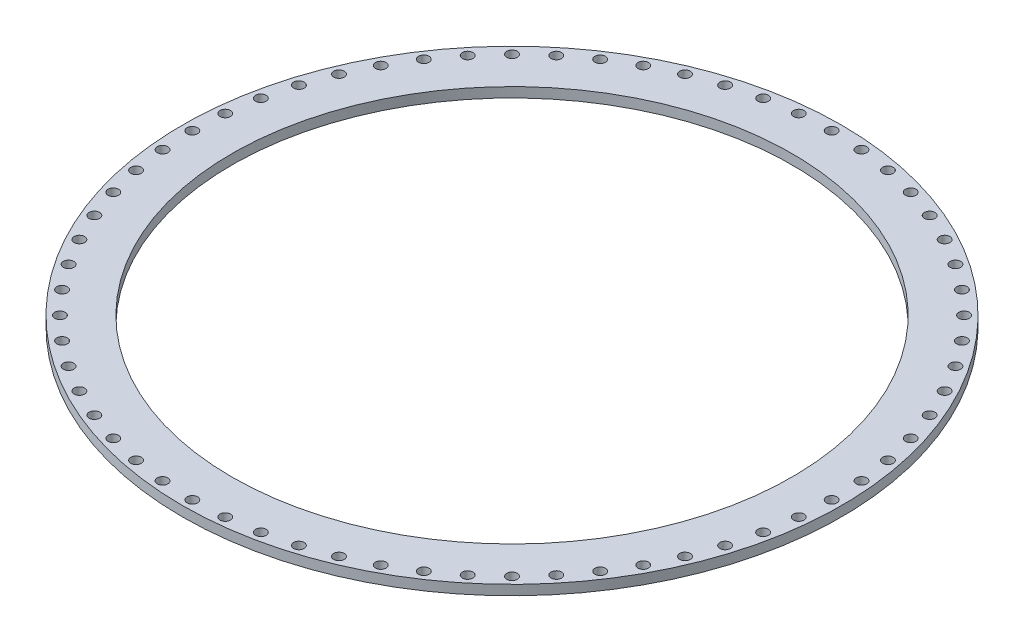
SolidWorks part; units mm, degrees
ref_plane "Front Plane" through (0, 0, 0) normal (0, 0, 1) x (1, 0, 0)
ref_plane "Top Plane" through (0, 0, 0) normal (0, 1, 0) x (1, 0, 0)
ref_plane "Right Plane" through (0, 0, 0) normal (1, 0, 0) x (0, 0, -1)
ref_axis "Axe1" through (0, 55, 0) along (0, -1, 0)
sketch "Esquisse2" plane through (0, 0, 0) normal (0, 0, 1) x (1, 0, 0)
  line L0 (0, 0) -> (100, 0)
  line L1 (100, 0) -> (100, 3)
  line L4 (100, 3) -> (0, 3)
  line L5 (0, 55) -> (0, -55) construction
  line L6 (0, 3) -> (0, 0)
  dimension "D1" = 100
  dimension "D3" = 3
revolve "MainRevolution" add sketch "Esquisse2" angle 360 about axis through (0, 55, 0) along (0, -1, 0)
sketch "Esquisse4" plane through (0, 3, 0) normal (0, 1, 0) x (1, 0, 0)
  circle A0 centre (0, 0) radius 85
  dimension "D1" = 170
extrude "CentralHole" cut sketch "Esquisse4" against normal through all
sketch "Esquisse5" plane through (0, 3, 0) normal (0, 1, 0) x (1, 0, 0)
  circle A0 centre (97, 0) radius 1.6
  dimension "D1" = 3.2
  dimension "D2" = 97
extrude "FixingHole" cut sketch "Esquisse5" against normal through all
pattern_circular "Répétition circulaire1" count 64 every 5.625 about axis through (0, 0, 0) along (0, 1, 0) of "FixingHole"
